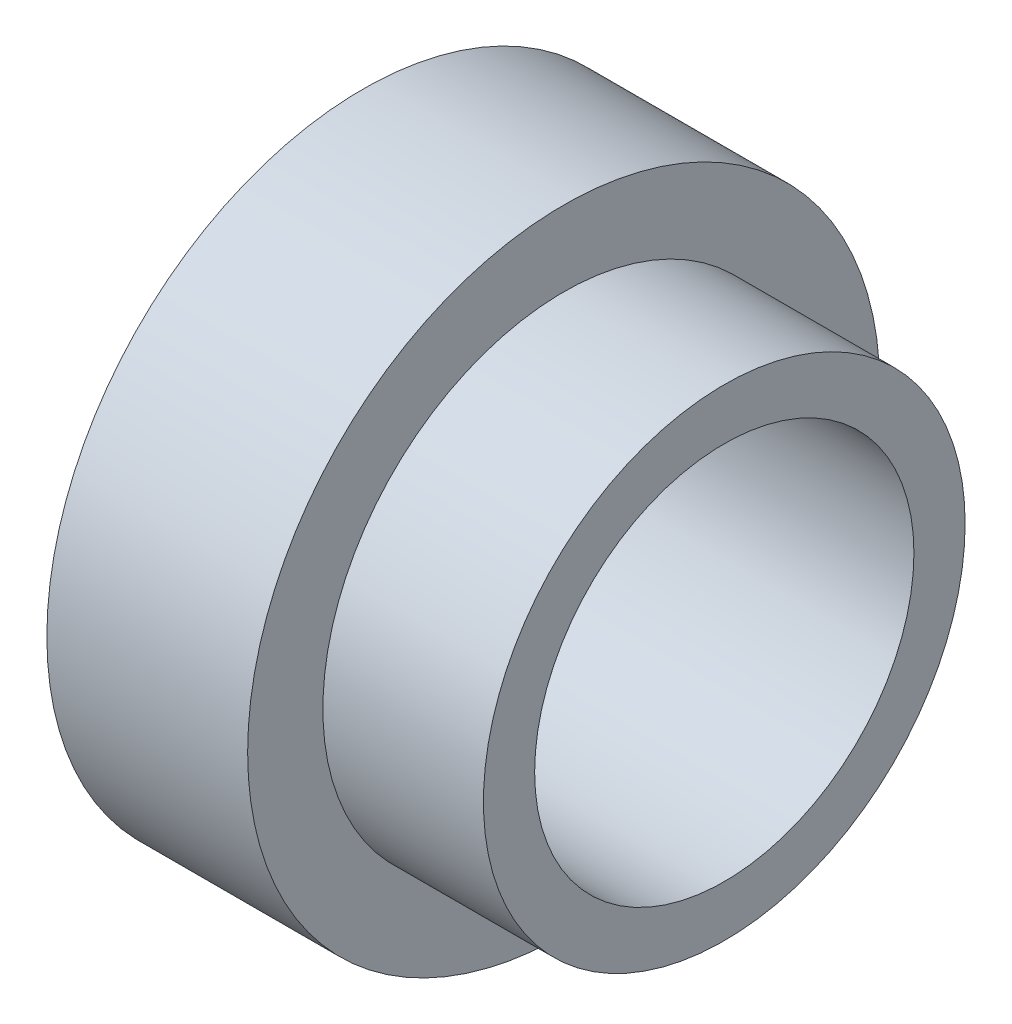
SolidWorks part; units mm, degrees
ref_plane "Front Plane" through (0, 0, 0) normal (0, 0, 1) x (1, 0, 0)
ref_plane "Top Plane" through (0, 0, 0) normal (0, 1, 0) x (1, 0, 0)
ref_plane "Right Plane" through (0, 0, 0) normal (1, 0, 0) x (0, 0, -1)
sketch "Sketch1" plane through (0, 0, 0) normal (1, 0, 0) x (0, 0, -1)
  circle A0 centre (0, 0) radius 12.5
  circle A1 centre (0, 0) radius 7.5
  dimension "D1" = 25
  dimension "D2" = 15
extrude "Boss-Extrude1" add sketch "Sketch1" along normal blind 7.94
sketch "Sketch2" plane through (7.94, 0, 0) normal (1, 0, 0) x (0, 0, -1)
  circle A0 centre (0, 0) radius 9.525
  circle A1 centre (0, 0) radius 7.5
  dimension "D1" = 19.05
extrude "Boss-Extrude2" add sketch "Sketch2" along normal blind 6.35
